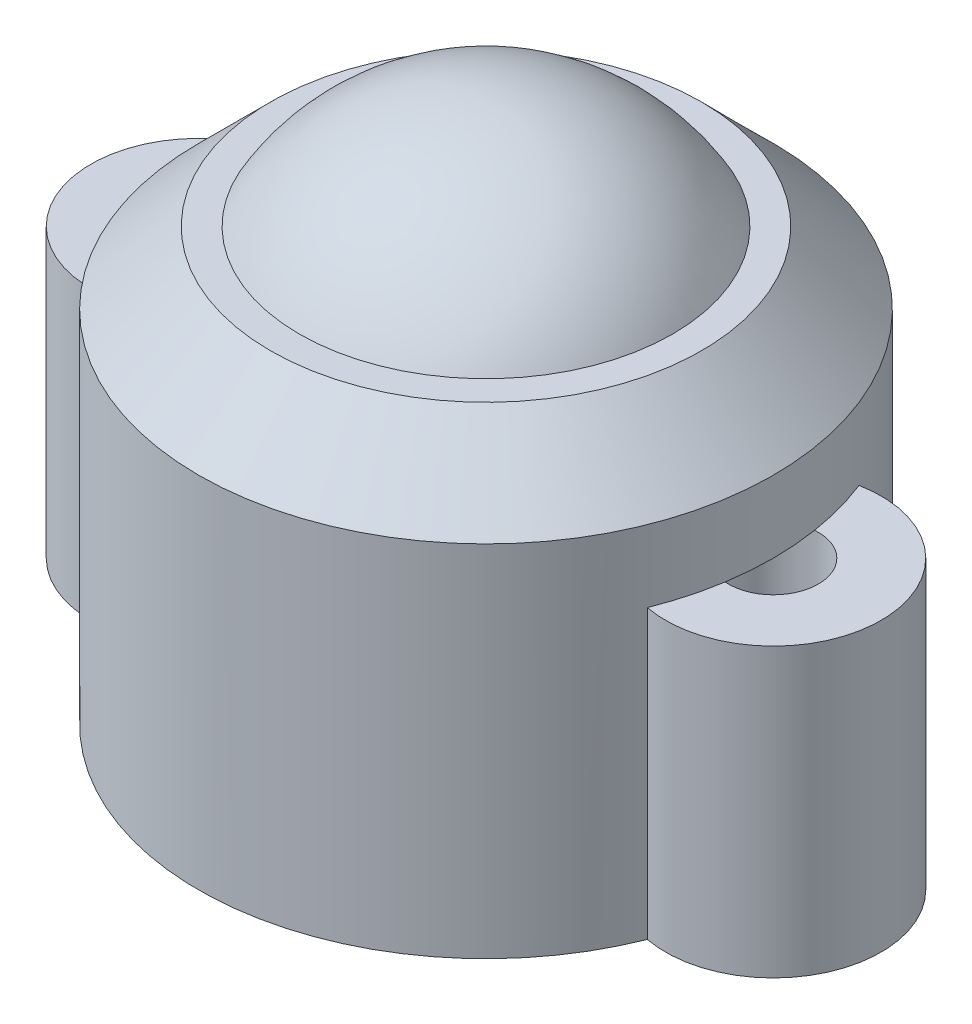
SolidWorks part; units mm, degrees
ref_plane "Front Plane" through (0, 0, 0) normal (0, 0, 1) x (1, 0, 0)
ref_plane "Top Plane" through (0, 0, 0) normal (0, 1, 0) x (1, 0, 0)
ref_plane "Right Plane" through (0, 0, 0) normal (1, 0, 0) x (0, 0, -1)
sketch "Sketch1" plane through (0, 0, 0) normal (0, 1, 0) x (1, 0, 0)
  line L0 (0, -55) -> (0, 55) construction
  circle A1 centre (8, 0) radius 1.25
  arc A2 (7.4375, -2.9468) -> (7.4375, 2.9468) centre (8, 0) ccw
  arc A3 (7.4375, 2.9468) -> (-7.4375, 2.9468) centre (0, 0) ccw
  circle A4 centre (-8, 0) radius 1.25
  arc A5 (-7.4375, -2.9468) -> (-7.4375, 2.9468) centre (-8, 0) cw
  arc A7 (-7.4375, -2.9468) -> (7.4375, -2.9468) centre (0, 0) ccw
  dimension "D2" = 2.5
  dimension "D3" = 6
extrude "Boss-Extrude1" add sketch "Sketch1" along normal blind 8
sketch "Sketch2" plane through (0, 8, 0) normal (0, 1, 0) x (1, 0, 0)
  circle A0 centre (0, 0) radius 8
extrude "Boss-Extrude2" add sketch "Sketch2" along normal blind 4
chamfer "Chamfer1" distance 2 angle 45 1 edges at (0, 12, 8)
sketch "Sketch3" plane through (0, 0, 0) normal (0, 0, 1) x (1, 0, 0)
  line L0 (0, 12) -> (0, 9) construction
  line L1 (6, 12) -> (-6, 12) construction
  line L2 (0, 15) -> (0, 3)
  arc A0 (0, 3) -> (0, 15) centre (0, 9) ccw
  dimension "D2" = 12
  dimension "D1" = 3
revolve "Revolve2" add sketch "Sketch3" angle 360 about L0
